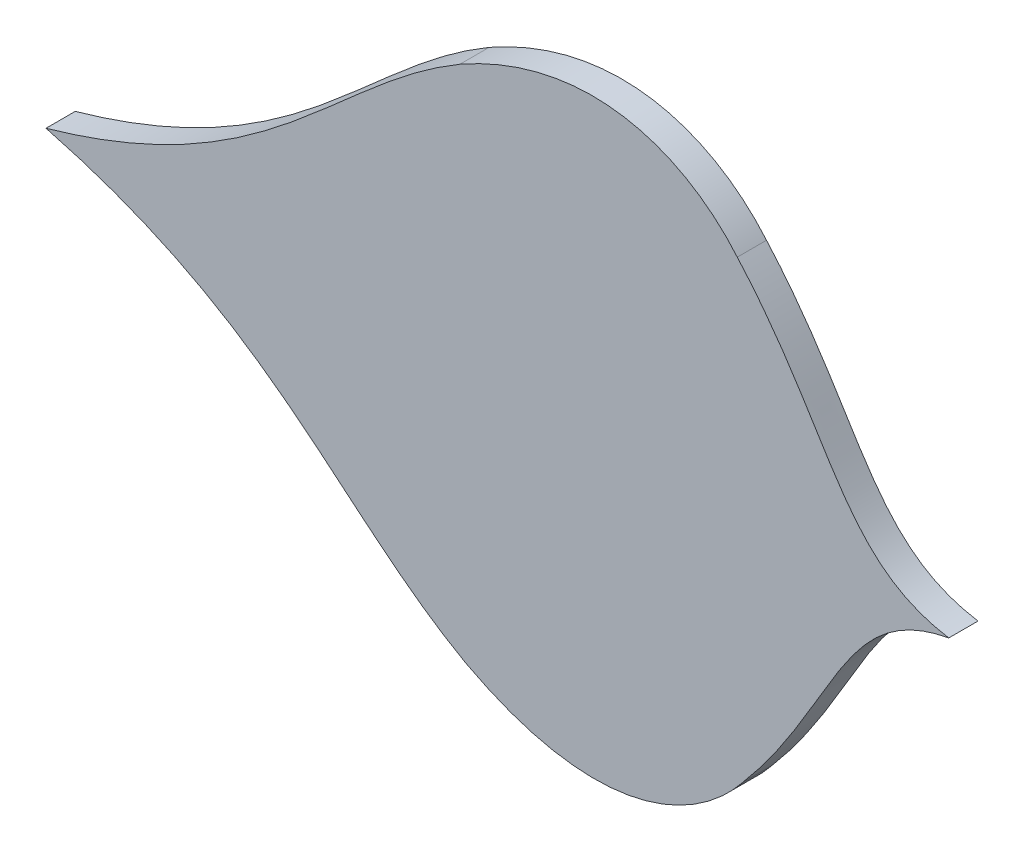
SolidWorks part; units mm, degrees
ref_plane "Front Plane" through (0, 0, 0) normal (0, 0, 1) x (1, 0, 0)
ref_plane "Top Plane" through (0, 0, 0) normal (0, 1, 0) x (1, 0, 0)
ref_plane "Right Plane" through (0, 0, 0) normal (1, 0, 0) x (0, 0, -1)
sketch "Sketch1" plane through (0, 0, 0) normal (0, 0, 1) x (1, 0, 0)
  line L0 (318.6667, 759.5) -> (1593.3333, 759.5) construction
  line L1 (1784.9094, 764.8406) -> (109.2028, 746.3245) construction
  spline S0 degree 3 poles (1416.341, 760.768) (1379.6881, 766.6771) (1376.7963, 800.7882) (1343.9641, 837.4286) knots 0 0 0 0 1 1 1 1
  spline S1 degree 3 poles (1343.9641, 837.4286) (1328.1662, 856.3002) (1295.2772, 873.1515) (1249.0743, 847.1623) knots 0 0 0 0 1 1 1 1
  spline S2 degree 3 poles (1249.0743, 847.1623) (1205.4489, 821.536) (1185.2989, 779.4535) (1107.4162, 757.3545) knots 0 0 0 0 1 1 1 1
  spline S3 degree 3 poles (1416.341, 760.768) (1379.8276, 754.0505) (1377.6903, 719.8838) (1345.6757, 682.5269) knots 0 0 0 0 1 1 1 1
  spline S4 degree 3 poles (1345.6757, 682.5269) (1330.2987, 663.3108) (1297.7901, 645.7369) (1251.0242, 670.6988) knots 0 0 0 0 1 1 1 1
  spline S5 degree 3 poles (1251.0242, 670.6988) (1206.8432, 695.3548) (1185.7682, 736.9819) (1107.4162, 757.3545) knots 0 0 0 0 1 1 1 1
extrude "Boss-Extrude1" add sketch "Sketch1" along normal blind 10
